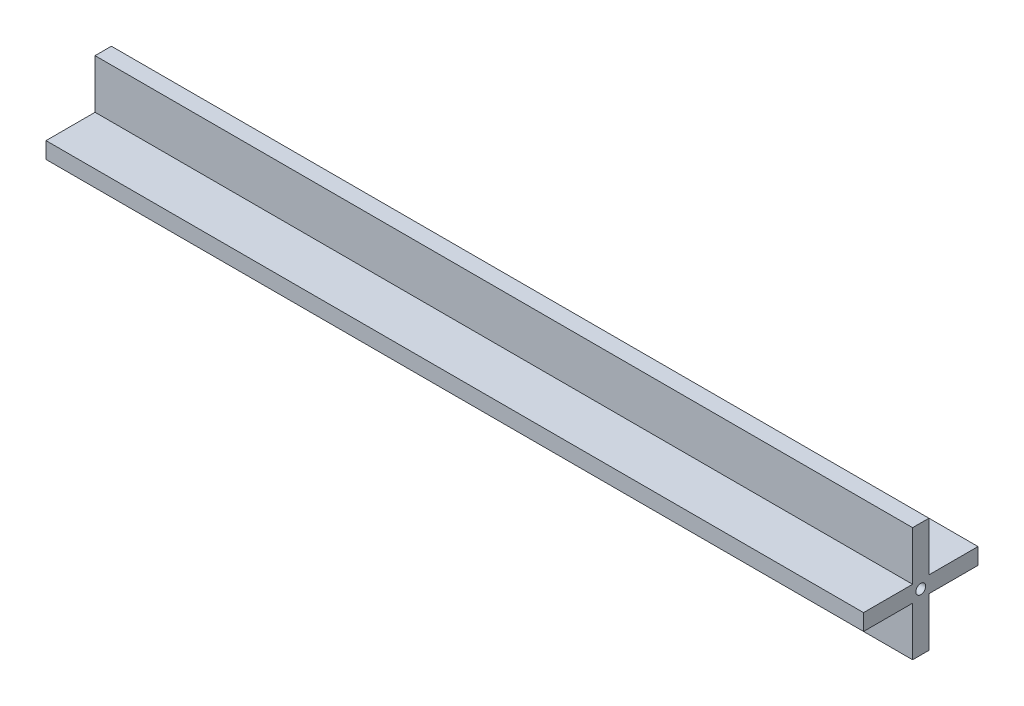
SolidWorks part; units mm, degrees
ref_plane "Front Plane" through (0, 0, 0) normal (0, 0, 1) x (1, 0, 0)
ref_plane "Top Plane" through (0, 0, 0) normal (0, 1, 0) x (1, 0, 0)
ref_plane "Right Plane" through (0, 0, 0) normal (1, 0, 0) x (0, 0, -1)
sketch "Sketch1" plane through (0, 0, 0) normal (1, 0, 0) x (0, 0, -1)
  line L0 (17.5, 2.5) -> (2.5, 2.5)
  line L1 (-2.5, 17.5) -> (2.5, 17.5)
  line L2 (-2.5, 17.5) -> (-2.5, 2.5)
  line L3 (-2.5, 2.5) -> (2.5, 2.5) construction
  line L4 (2.5, 17.5) -> (2.5, 2.5)
  line L5 (-2.5, 17.5) -> (2.5, 2.5) construction
  line L6 (-2.5, 2.5) -> (2.5, 17.5) construction
  line L7 (17.5, -2.5) -> (2.5, -2.5)
  line L8 (17.5, 2.5) -> (17.5, -2.5)
  line L9 (2.5, -17.5) -> (2.5, -2.5)
  line L10 (-2.5, -17.5) -> (-2.5, -2.5)
  line L11 (2.5, -17.5) -> (-2.5, -17.5)
  line L12 (-17.5, -2.5) -> (-2.5, -2.5)
  line L13 (-17.5, 2.5) -> (-2.5, 2.5)
  line L14 (-17.5, -2.5) -> (-17.5, 2.5)
  circle A0 centre (0, 0) radius 1.5
  point P0 (0, 10)
  point P5 (0, 0)
  point P22 (0, 0)
  dimension "D5" = 3
  dimension "D1" = 5
  dimension "D2" = 15
  dimension "D3" = 2.5
  dimension "D4" = 4
extrude "Boss-Extrude1" add sketch "Sketch1" along normal blind 250
